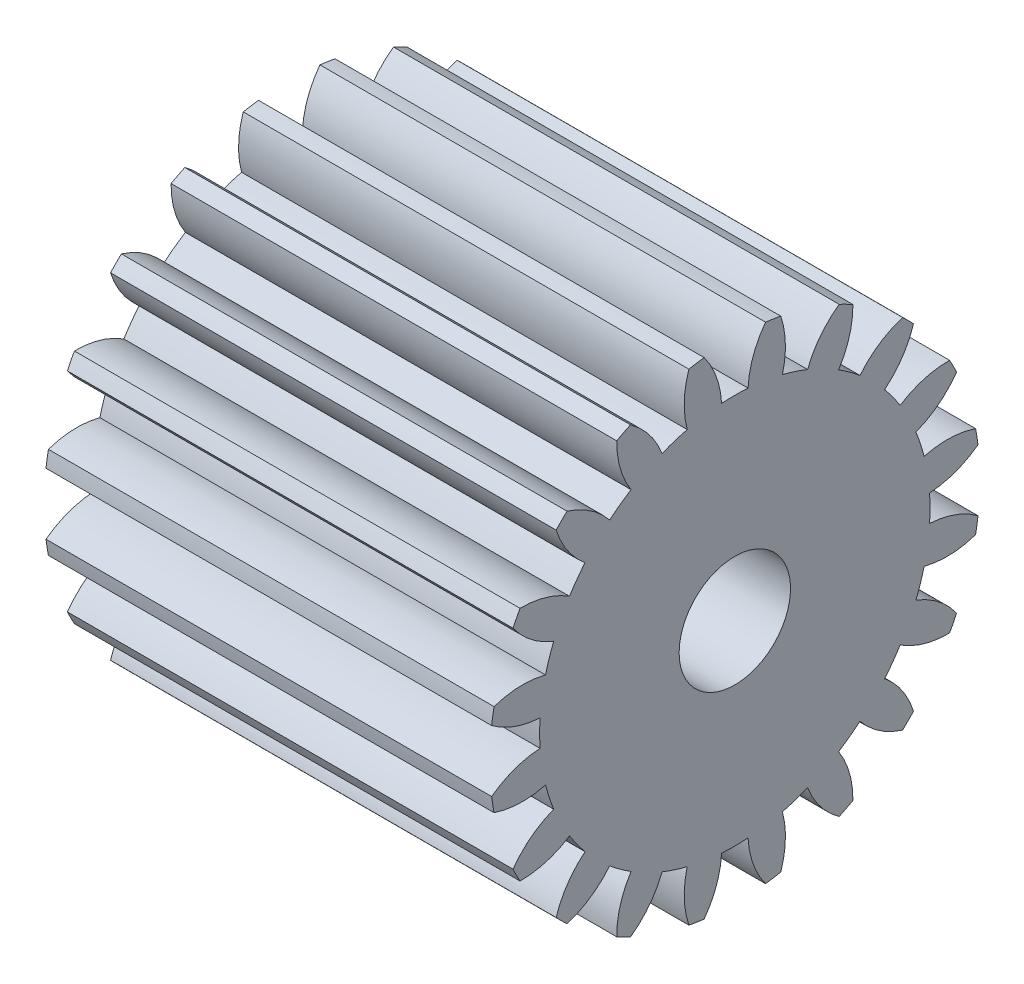
SolidWorks part; units mm, degrees
ref_plane "Plane1" through (0, 0, 0) normal (0, 0, 1) x (1, 0, 0)
ref_plane "Plane2" through (0, 0, 0) normal (0, 1, 0) x (1, 0, 0)
ref_plane "Plane3" through (0, 0, 0) normal (1, 0, 0) x (0, 0, -1)
other "Configuration Table"
sketch "HoldingSke" plane through (0, 0, 0) normal (0, 1, 0) x (1, 0, 0)
  line L0 (0, 0) -> (477.3639, -173.7462)
  line L1 (-15, 0) -> (100, 0) construction
  line L2 (0, 0) -> (-2.1039, 2.3779)
  line L3 (0, 0) -> (-11.863, 4.5341)
  line L4 (0, 0) -> (8.1152, 2.9537)
  line L5 (0, 0) -> (-47.5972, -17.7524)
  line L6 (0, 0) -> (-21.0557, -14.2063)
  line L7 (-2.1039, 2.3779) -> (8.8308, 51.9871)
  line L8 (-76.2, 54.61) -> (-69.596, 54.61)
  line L9 (-67.7845, 28.3722) -> (-49.3413, 33.142)
  line L10 (-76.2, 71.12) -> (104.1128, 71.12)
  line L11 (0, 0) -> (-25.4, 0)
  line L12 (-76.2, 101.6) -> (-76.1492, 101.6)
  line L13 (24.9733, 27.94) -> (52.9518, 28.4284)
  line L14 (24.9733, 27.94) -> (25.0241, 27.9398)
  line L15 (24.9733, 27.94) -> (100.4021, 29.52)
  circle A0 centre (0, 0) radius 3.175
  circle A1 centre (0, 0) radius 11.1252
  circle A2 centre (0, 0) radius 38.1
  circle A3 centre (0, 0) radius 3.175
  dimension "MHD" = 22.2504
  dimension "Hub_dia" = 76.2
  dimension "Bore" = 6.35
  dimension "MBD" = 6.35
  dimension "Num_teeth" = 20
  dimension "Pitch" = 508
  dimension "Overall_len" = 50.8
  dimension "Show_teeth" = 20
  dimension "Thickness" = 25.4
  dimension "OAL" = 50.8001
  dimension "T_dim" = 6.604
  dimension "Ap" = 14.5
  dimension "H" = 19.05
  dimension "Pitch_radius" = 180.3128
  dimension "Width" = 25.4
  dimension "Backlash" = 0.0508
  dimension "Addendum_fac" = 1
  dimension "Dedendum_fac" = 1.2
  dimension "Clearance_fac" = 0.2
  dimension "Dedendum_add" = 0.0508
sketch "BasProSke" plane through (0, 0, 0) normal (0, 1, 0) x (1, 0, 0)
  line L0 (-10, 0) -> (60, 0) construction
  line L1 (0, 0) -> (0, 13.97)
  line L2 (0, 0) -> (25.4, 0)
  line L3 (25.4, 0) -> (25.4, 13.97)
  line L4 (25.4, 13.97) -> (0, 13.97)
  dimension "Thickness" = 25.4
  dimension "Diameter" = 27.94
revolve "Base-Revolve" add sketch "BasProSke" angle 360 about L0
sketch "TooCutSke" plane through (0, 0, 0) normal (1, 0, 0) x (0, 0, -1)
  line L1 (0, 0) -> (0, 107) construction
  line L2 (0, 0) -> (-1.0853, 12.6535) construction
  line L3 (0, 0) -> (-3.9633, 25.0231) construction
  line L4 (-1.0853, 12.6535) -> (-1.9816, 12.5116) construction
  arc A0 (0.7531, 11.0997) -> (-0.7531, 11.0997) centre (0, 0) ccw
  arc A1 (1.7676, 13.8833) -> (-1.7676, 13.8833) centre (0, 0) ccw
  circle A2 centre (0, 0) radius 12.7 construction
  circle A3 centre (0, 0) radius 12.2955 construction
  arc A4 (-0.7531, 11.0997) -> (-1.7676, 13.8833) centre (-5.8258, 10.8277) ccw
  arc A5 (1.7676, 13.8833) -> (0.7531, 11.0997) centre (5.8258, 10.8277) ccw
  dimension "Root_dia" = 22.2504
  dimension "Overcut_dia" = 27.9908
  dimension "Pitch_dia" = 25.4
  dimension "Base_dia" = 24.591
  dimension "Flank_rad" = 5.08
  dimension "Half_ang" = 9
  dimension "Half_CT" = 0.9075
extrude "ToothCut" cut sketch "TooCutSke" along normal through all
fillet "Breaks" [suppressed] radius 0.0254
fillet "RootFillets" [suppressed] radius 0.3048
pattern_circular "TeethCuts" count 20 every 18 about axis through (-10, 0, 0) along (1, 0, 0) of "ToothCut", "RootFillets", "Breaks"
sketch "HubNeaOneSke" plane through (0, 0, 0) normal (-1, 0, 0) x (0, 0, 1)
  circle A0 centre (0, 0) radius 11.1252
  dimension "Diameter" = 22.2504
extrude "HubNearOne" [suppressed] add sketch "HubNeaOneSke" along normal blind 25.4001
sketch "HubNeaBotSke" plane through (0, 0, 0) normal (-1, 0, 0) x (0, 0, 1)
  circle A0 centre (0, 0) radius 11.1252
  dimension "Diameter" = 22.2504
extrude "HubNearBoth" [suppressed] add sketch "HubNeaBotSke" along normal blind 12.7
ref_plane "FarPln" through (25.4, 0, 0) normal (1, 0, 0) x (0, 0, -1)
sketch "HubFarSke" plane through (25.4, 0, 0) normal (1, 0, 0) x (0, 0, -1)
  circle A0 centre (0, 0) radius 11.1252
  dimension "Diameter" = 22.2504
extrude "HubFar" [suppressed] add sketch "HubFarSke" along normal blind 12.7
sketch "BorSke" plane through (0, 0, 0) normal (1, 0, 0) x (0, 0, -1)
  circle A0 centre (0, 0) radius 3.175
  dimension "Diameter" = 6.35
extrude "Bore" cut sketch "BorSke" along normal mid plane 101.6001
sketch "KeySke" plane through (0, 0, 0) normal (1, 0, 0) x (0, 0, -1)
  line L0 (-0.127, 0) -> (-0.127, 3.429)
  line L1 (-0.127, 3.429) -> (0.127, 3.429)
  line L2 (0.127, 3.429) -> (0.127, 0)
  line L3 (0, 0) -> (0, 34) construction
  line L4 (-0.127, 0) -> (0.127, 0)
  dimension "Offset" = 3.429
  dimension "Width" = 0.254
extrude "Keyway" [suppressed] cut sketch "KeySke" along normal mid plane 101.6001
pattern_circular "Keyway2" [suppressed] count 2 every 90 about axis through (-10, 0, 0) along (1, 0, 0)
equation "' \"Pitch@HoldingSke\" = 4"
equation "' \"Num_teeth@HoldingSke\" = 12"
equation "' \"Ap@HoldingSke\" =  20"
equation "' \"Ap@HoldingSke\" = 20"
equation "' \"Width@HoldingSke\" = 0.5"
equation "' \"Hub_dia@HoldingSke\"= 1"
equation "' \"Hub_dia@HoldingSke\" = 1"
equation "' \"Overall_len@HoldingSke\" = 1.0"
equation "' \"Bore@HoldingSke\" = 0.75"
equation "' \"T_dim@HoldingSke\" = 0.85"
equation "' \"Width@KeySke\" = 0.25"
equation "' \"Show_teeth@HoldingSke\" = 13"
equation "' \"Backlash@HoldingSke\" = 0.009"
equation "' \"Addendum_fac@HoldingSke\" = 1.0"
equation "' \"Dedendum_fac@HoldingSke\" = 1.25"
equation "' \"Dedendum_add@HoldingSke\" = 0.00005"
equation "' \"Clearance_fac@HoldingSke\" = 0.25"
equation "' \"Pitch@HoldingSke\" = 0.5"
equation "' \"Num_teeth@HoldingSke\" = 23"
equation "' \"Show_teeth@HoldingSke\" = 23"
equation "' \"Backlash@HoldingSke\" = 0.0375"
equation "\"Overcut_dia@TooCutSke\" = (\"Num_teeth@HoldingSke\" + 2 * \"Addendum_fac@HoldingSke\") / \"Pitch@HoldingSke\" + 0.002"
equation "\"Pitch_dia@TooCutSke\" = \"Num_teeth@HoldingSke\" / \"Pitch@HoldingSke\""
equation "\"Base_dia@TooCutSke\" = \"Num_teeth@HoldingSke\" / \"Pitch@HoldingSke\" * cos((\"Ap@HoldingSke\"  * 3.14159265 / 180))"
equation "\"Root_dia@TooCutSke\" = (\"Num_teeth@HoldingSke\" + 2) / \"Pitch@HoldingSke\" - 2 * (\"Addendum_fac@HoldingSke\" + \"Dedendum_fac@HoldingSke\") / \"Pitch@HoldingSke\" - \"Dedendum_add@HoldingSke\" * 2"
equation "\"Half_ang@TooCutSke\" = 180 / \"Num_teeth@HoldingSke\""
equation "\"Half_CT@TooCutSke\" = \"Num_teeth@HoldingSke\" / \"Pitch@HoldingSke\" * sin((3.14159265 / 2 / \"Num_teeth@HoldingSke\")) / 2 - 7 * \"Backlash@HoldingSke\" / 4"
equation "\"Flank_rad@TooCutSke\" = \"Num_teeth@HoldingSke\" / \"Pitch@HoldingSke\" / 5"
equation "\"Radius@RootFillets\" = \"Clearance_fac@HoldingSke\" / \"Pitch@HoldingSke\" + \"Dedendum_add@HoldingSke\""
equation "\"Break_rad@Breaks\" = 0.02 / \"Pitch@HoldingSke\""
equation "\"Thickness@HoldingSke\" = \"Width@HoldingSke\""
equation "\"OAL@HoldingSke\" = \"Thickness@HoldingSke\""
equation "\"MHD@HoldingSke\" = (\"Num_teeth@HoldingSke\" + 2) / \"Pitch@HoldingSke\" - 2 * (\"Addendum_fac@HoldingSke\" + \"Dedendum_fac@HoldingSke\")  / \"Pitch@HoldingSke\" - \"Dedendum_add@HoldingSke\" * 2"
equation "\"MBD@HoldingSke\" = (\"Num_teeth@HoldingSke\" + 2) / \"Pitch@HoldingSke\" - 2 * (\"Addendum_fac@HoldingSke\" + \"Dedendum_fac@HoldingSke\")  / \"Pitch@HoldingSke\" - \"Dedendum_add@HoldingSke\" * 2 - 0.002"
equation "\"MHD@HoldingSke\" = ((sgn( \"MHD@HoldingSke\" - \"Hub_dia@HoldingSke\" )-1)*( \"MHD@HoldingSke\" - \"Hub_dia@HoldingSke\" ))/-2+ \"Hub_dia@HoldingSke\""
equation "\"MBD@HoldingSke\" = ((sgn( \"MBD@HoldingSke\" - \"Bore@HoldingSke\" )-1)*( \"MBD@HoldingSke\" - \"Bore@HoldingSke\" ))/-2+ \"Bore@HoldingSke\""
equation "\"OAL@HoldingSke\" = ((sgn( \"OAL@HoldingSke\" - \"Overall_len@HoldingSke\" )+1)*( \"OAL@HoldingSke\" - \"Overall_len@HoldingSke\" ))/2 + \"Overall_len@HoldingSke\" + 0.000002"
equation "\"Num_teeth@TeethCuts\" = int( \"Show_teeth@HoldingSke\" ) + 1"
equation "\"Num_teeth@TeethCuts\" = ((sgn( \"Num_teeth@TeethCuts\" - \"Num_teeth@HoldingSke\" )-1)*( \"Num_teeth@TeethCuts\" - \"Num_teeth@HoldingSke\" ))/-2+ \"Num_teeth@HoldingSke\""
equation "\"Num_teeth@TeethCuts\" = ((sgn( \"Num_teeth@TeethCuts\" - 2.0)+1)*( \"Num_teeth@TeethCuts\" - 2.0))/2 +2.0"
equation "\"Angle@TeethCuts\" = 360.0 / \"Num_teeth@HoldingSke\""
equation "\"Diameter@BasProSke\" = (\"Num_teeth@HoldingSke\" + 2 * \"Addendum_fac@HoldingSke\") / \"Pitch@HoldingSke\""
equation "\"Thickness@BasProSke\"  = \"Thickness@HoldingSke\""
equation "' \"Fillet_rad@BasProSke\" =  \"Thickness@HoldingSke\" * 0.05"
equation "' \"Fillet_rad@BasProSke\" = \"Thickness@HoldingSke\" * 0.05"
equation "\"MHD@HoldingSke\" = ((sgn( \"MHD@HoldingSke\" - \"Root_dia@TooCutSke\" )-1)*( \"MHD@HoldingSke\" - \"Root_dia@TooCutSke\" ))/-2+ \"Root_dia@TooCutSke\""
equation "\"Diameter@HubNeaOneSke\" = \"MHD@HoldingSke\""
equation "\"Length@HubNearOne\" = \"OAL@HoldingSke\" - \"Thickness@BasProSke\""
equation "\"Diameter@HubNeaBotSke\" = \"MHD@HoldingSke\""
equation "\"Length@HubNearBoth\" = ( \"OAL@HoldingSke\" - \"Thickness@BasProSke\" ) / 2.0"
equation "\"Thickness@FarPln\" = \"Thickness@BasProSke\""
equation "\"Diameter@HubFarSke\" = \"MHD@HoldingSke\""
equation "\"Length@HubFar\" = ( \"OAL@HoldingSke\" - \"Thickness@BasProSke\" ) / 2.0"
equation "\"Diameter@BorSke\" = \"MBD@HoldingSke\""
equation "\"D1@Bore\" = \"OAL@HoldingSke\" * 2.0"
equation "\"D1@Keyway\" = \"OAL@HoldingSke\" * 2.0"
equation "\"Offset@KeySke\" = \"T_dim@HoldingSke\" - \"MBD@HoldingSke\" / 2.0"
